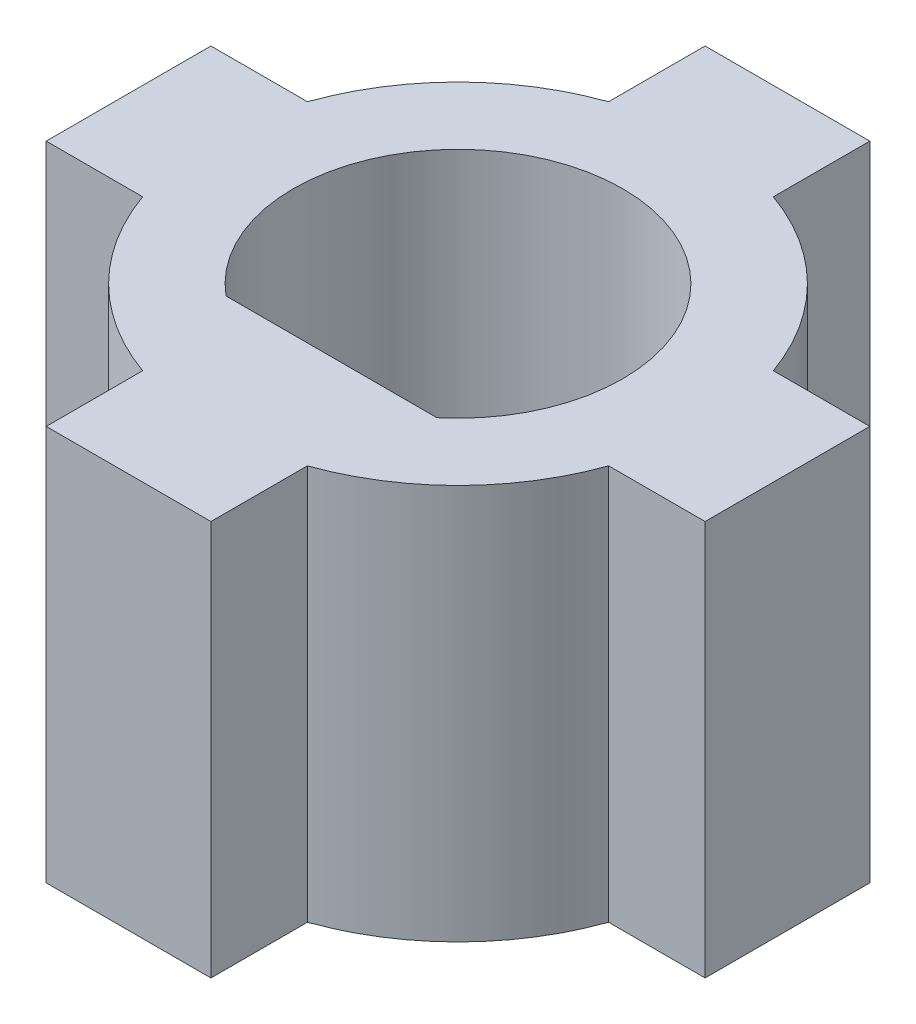
SolidWorks part; units mm, degrees
ref_plane "Front Plane" through (0, 0, 0) normal (0, 0, 1) x (1, 0, 0)
ref_plane "Top Plane" through (0, 0, 0) normal (0, 1, 0) x (1, 0, 0)
ref_plane "Right Plane" through (0, 0, 0) normal (1, 0, 0) x (0, 0, -1)
sketch "Sketch3" plane through (0, 0, 0) normal (0, 1, 0) x (1, 0, 0)
  line L0 (2.032, -2.4396) -> (-2.032, -2.4396)
  line L1 (1.5875, 0) -> (-1.5875, 0)
  line L2 (1.5875, 0) -> (1.5875, -6.35)
  line L3 (-1.5875, 0) -> (-1.5875, -6.35)
  line L4 (1.5875, -6.35) -> (-1.5875, -6.35)
  line L5 (1.5875, 0) -> (-1.5875, -6.35) construction
  line L6 (-1.5875, 0) -> (1.5875, -6.35) construction
  line L7 (0, -1.5875) -> (0, 1.5875)
  line L8 (0, -1.5875) -> (6.35, -1.5875)
  line L9 (0, 1.5875) -> (6.35, 1.5875)
  line L10 (6.35, -1.5875) -> (6.35, 1.5875)
  line L11 (0, -1.5875) -> (6.35, 1.5875) construction
  line L12 (0, 1.5875) -> (6.35, -1.5875) construction
  line L13 (1.5875, 0) -> (-1.5875, 0)
  line L14 (1.5875, 0) -> (1.5875, 6.35)
  line L15 (-1.5875, 0) -> (-1.5875, 6.35)
  line L16 (1.5875, 6.35) -> (-1.5875, 6.35)
  line L17 (1.5875, 0) -> (-1.5875, 6.35) construction
  line L18 (-1.5875, 0) -> (1.5875, 6.35) construction
  line L19 (0, 1.5875) -> (0, -1.5875)
  line L20 (0, 1.5875) -> (-6.35, 1.5875)
  line L21 (0, -1.5875) -> (-6.35, -1.5875)
  line L22 (-6.35, 1.5875) -> (-6.35, -1.5875)
  line L23 (0, 1.5875) -> (-6.35, -1.5875) construction
  line L24 (0, -1.5875) -> (-6.35, 1.5875) construction
  circle A0 centre (0, 0) radius 3.175
  circle A1 centre (0, 0) radius 1.5875 construction
  circle A2 centre (0, 0) radius 4.7625
  point P12 (0, -3.175)
  point P17 (3.175, 0)
  point P20 (0, 3.175)
  point P23 (-3.175, 0)
  dimension "D1" = 6.35
  dimension "D3" = 3.175
  dimension "D5" = 6.35
  dimension "D6" = 6.35
  dimension "D7" = 6.35
  dimension "D8" = 9.525
  dimension "D2" = 4.064
  dimension "D4" = 6.35
extrude "Boss-Extrude3" add sketch "Sketch3" along normal blind 7.62 contours A2 L14 L16 L15 | A2 L20 L22 L21 | L15 A2 L20 A0 | L20 A2 L21 A0 | L14 A2 L15 A0 | L9 A2 L14 A0 | A2 L8 L10 L9 | L8 A2 L9 A0 | L21 A2 L3 A0 | L0 A0 L3 | L3 A0 L2 L0 | L2 A0 L0 | L2 A2 L8 A0 | L3 A2 L2 A0 | A2 L3 L4 L2
